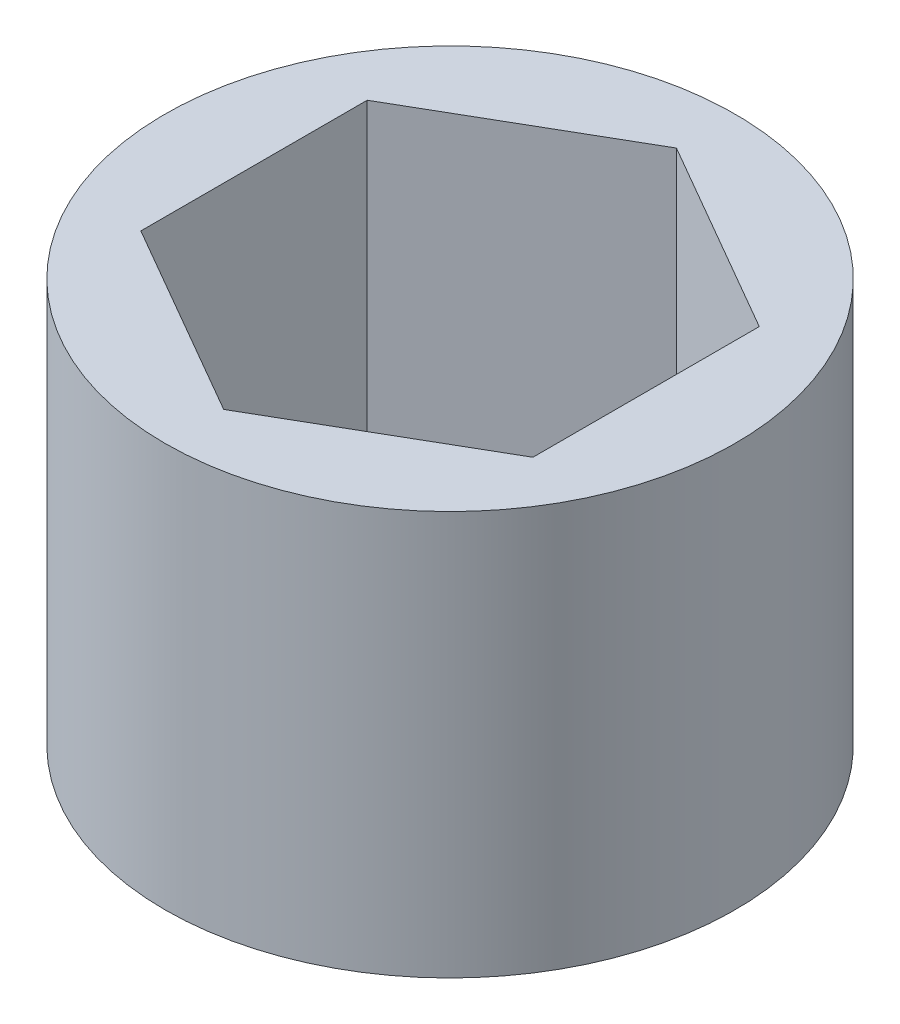
SolidWorks part; units mm, degrees
material "ABS"
ref_plane "Front Plane" through (0, 0, 0) normal (0, 0, 1) x (1, 0, 0)
ref_plane "Top Plane" through (0, 0, 0) normal (0, 1, 0) x (1, 0, 0)
ref_plane "Right Plane" through (0, 0, 0) normal (1, 0, 0) x (0, 0, -1)
sketch "Sketch1" plane through (0, 0, 0) normal (0, 1, 0) x (1, 0, 0)
  line L1 (0, 7.5615) -> (-6.5484, 3.7807)
  line L2 (-6.5484, 3.7807) -> (-6.5484, -3.7807)
  line L3 (-6.5484, -3.7807) -> (0, -7.5615)
  line L4 (0, -7.5615) -> (6.5484, -3.7807)
  line L5 (6.5484, -3.7807) -> (6.5484, 3.7807)
  line L6 (6.5484, 3.7807) -> (0, 7.5615)
  circle A0 centre (0, 0) radius 6.5484 construction
  circle A1 centre (0, 0) radius 9.525
  dimension "D1" = 13.0969
  dimension "D2" = 19.05
extrude "Boss-Extrude1" add sketch "Sketch1" along normal blind 13.4937
